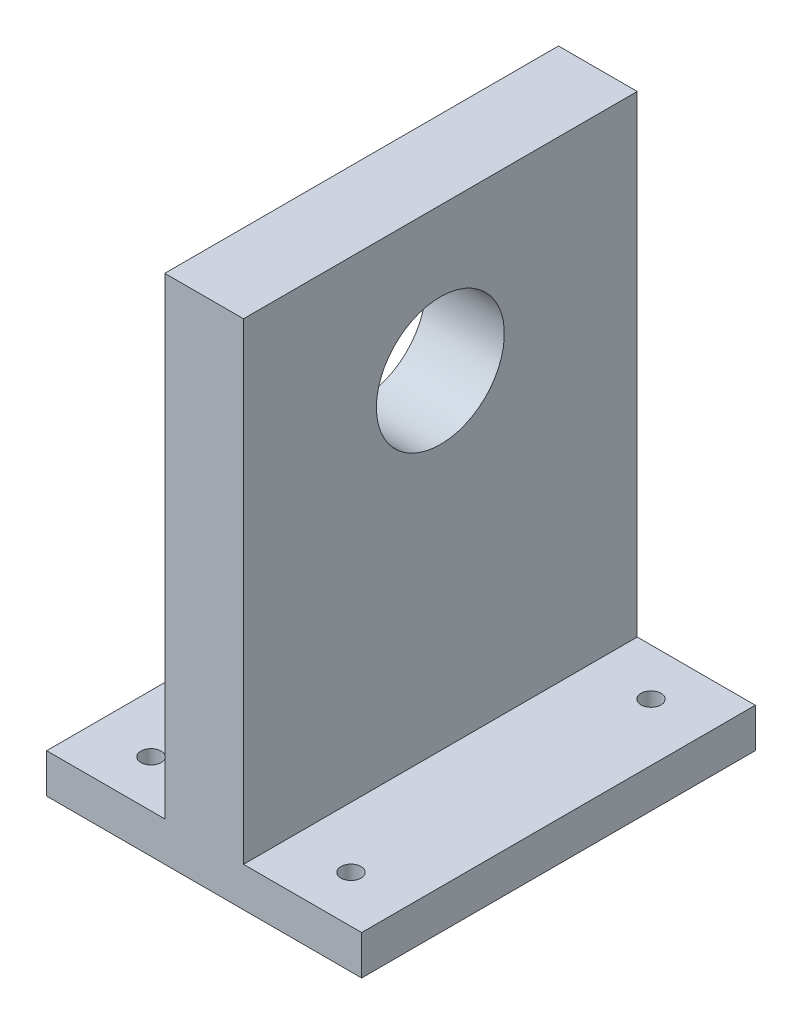
SolidWorks part; units mm, degrees
ref_plane "Front Plane" through (0, 0, 0) normal (0, 0, 1) x (1, 0, 0)
ref_plane "Top Plane" through (0, 0, 0) normal (0, 1, 0) x (1, 0, 0)
ref_plane "Right Plane" through (0, 0, 0) normal (1, 0, 0) x (0, 0, -1)
sketch "Sketch2" plane through (0, 0, 0) normal (0, 1, 0) x (1, 0, 0)
  line L1 (-40, -50) -> (40, -50)
  line L2 (-40, -50) -> (-40, 50)
  line L3 (-40, 50) -> (40, 50)
  line L4 (40, -50) -> (40, 50)
  line L5 (-40, -50) -> (40, 50) construction
  line L6 (-40, 50) -> (40, -50) construction
  point P0 (0, 0)
  dimension "D1" = 100
  dimension "D2" = 80
extrude "Boss-Extrude1" add sketch "Sketch2" along normal blind 10 contours L2 L3 L4 L1
sketch "Sketch3" plane through (0, 10, 0) normal (0, 1, 0) x (1, 0, 0)
  line L0 (-40, 50) -> (40, 50) construction
  line L1 (-10, -50) -> (10, -50)
  line L2 (-10, -50) -> (-10, 50)
  line L3 (-10, 50) -> (10, 50)
  line L4 (10, -50) -> (10, 50)
  line L5 (-10, -50) -> (10, 50) construction
  line L6 (-10, 50) -> (10, -50) construction
  point P0 (0, 0)
  dimension "D1" = 20
extrude "Boss-Extrude2" add sketch "Sketch3" along normal blind 120
sketch "Sketch4" plane through (-10, 0, 0) normal (-1, 0, 0) x (0, 0, 1)
  line L0 (0, 130) -> (0, 0) construction
  line L1 (-50, 130) -> (50, 130) construction
  line L2 (-50, 93.5871) -> (50, 93.5871) construction
  line L3 (-50, 130) -> (-50, 10) construction
  line L4 (50, 130) -> (50, 10) construction
  line L5 (50, 0) -> (-50, 0) construction
  circle A0 centre (0, 93.5871) radius 0.75 construction
  circle A2 centre (0, 93.5871) radius 16.25
  point P13 (0, 93.5871)
  dimension "D6" = 1.5
  dimension "D1" = 32.5
  dimension "D8" = 93.5871
sketch "Sketch5" plane through (0, 0, 0) normal (0, -1, 0) x (1, 0, 0)
  line L0 (0, 50) -> (0, -50) construction
  line L1 (-40, 50) -> (40, 50) construction
  line L2 (-40, -50) -> (40, -50) construction
  line L3 (-40, 0) -> (40, 0) construction
  line L4 (-40, 50) -> (-40, -50) construction
  line L5 (40, 50) -> (40, -50) construction
  line L6 (-40, 38.1) -> (40, 38.1) construction
  line L7 (-40, -38.1) -> (40, -38.1) construction
  line L8 (-25.4, 50) -> (-25.4, -50) construction
  line L9 (25.4, 50) -> (25.4, -50) construction
  circle A0 centre (-25.4, -38.1) radius 2.555
  circle A1 centre (25.4, -38.1) radius 2.555
  circle A2 centre (-25.4, 38.1) radius 2.555
  circle A3 centre (25.4, 38.1) radius 2.555
  dimension "D5" = 5.11
  dimension "D1" = 76.2
  dimension "D2" = 38.1
  dimension "D3" = 50.8
  dimension "D4" = 25.4
extrude "Cut-Extrude2" cut sketch "Sketch5" against normal blind 55 contours A2 | A0 | A1 | A3
extrude "Cut-Extrude4" cut sketch "Sketch4" against normal blind 45 contours A2
